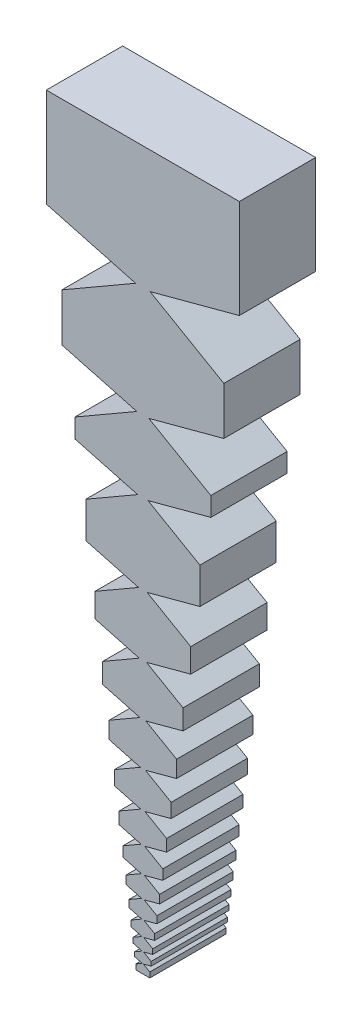
SolidWorks part; units mm, degrees
ref_plane "Front Plane" through (0, 0, 0) normal (0, 0, 1) x (1, 0, 0)
ref_plane "Top Plane" through (0, 0, 0) normal (0, 1, 0) x (1, 0, 0)
ref_plane "Right Plane" through (0, 0, 0) normal (1, 0, 0) x (0, 0, -1)
sketch "spiral_flat" plane through (0, 0, 0) normal (0, 0, 1) x (1, 0, 0)
  line L0 (0, 93.979) -> (0, 0) construction
  line L1 (0.9137, 0) -> (-0.9137, 0) construction
  line L2 (1.0887, 1.1616) -> (-1.0887, 1.1616) construction
  line L3 (1.2971, 2.5456) -> (-1.2971, 2.5456) construction
  line L4 (1.5454, 4.1945) -> (-1.5454, 4.1945) construction
  line L5 (1.8413, 6.1592) -> (-1.8413, 6.1592) construction
  line L6 (2.1938, 8.4999) -> (-2.1938, 8.4999) construction
  line L7 (2.6138, 11.2888) -> (-2.6138, 11.2888) construction
  line L8 (3.1142, 14.6116) -> (-3.1142, 14.6116) construction
  line L9 (3.7103, 18.5706) -> (-3.7103, 18.5706) construction
  line L10 (4.4207, 23.2874) -> (-4.4207, 23.2874) construction
  line L11 (5.267, 28.9073) -> (-5.267, 28.9073) construction
  line L12 (6.2753, 35.6031) -> (-6.2753, 35.6031) construction
  line L13 (7.4767, 43.5808) -> (-7.4767, 43.5808) construction
  line L14 (8.9081, 54.0582) -> (-8.9081, 54.0582) construction
  line L15 (10.6135, 63.438) -> (-10.6135, 63.438) construction
  line L16 (12.6455, 77.9031) -> (-12.6455, 77.9031) construction
  line L17 (15.0664, 93.979) -> (-15.0664, 93.979) construction
  line L18 (0, -0.6888) -> (0, 94.3287) construction
  line L19 (-0.9137, 0) -> (-15.0664, 93.979) construction
  line L20 (-12.6455, 77.9031) -> (-12.6455, 93.979) construction
  line L21 (-10.6135, 63.438) -> (-10.6135, 77.9031) construction
  line L22 (-8.9081, 54.0582) -> (-8.9081, 63.438) construction
  line L23 (-7.4767, 43.5808) -> (-7.4767, 54.0582) construction
  line L24 (-6.2753, 35.6031) -> (-6.2753, 43.5808) construction
  line L25 (-5.267, 28.9073) -> (-5.267, 35.6031) construction
  line L26 (-4.4207, 23.2874) -> (-4.4207, 28.9073) construction
  line L27 (-3.7103, 18.5706) -> (-3.7103, 23.2874) construction
  line L28 (-3.1142, 14.6116) -> (-3.1142, 18.5706) construction
  line L29 (-2.6138, 11.2888) -> (-2.6138, 14.6116) construction
  line L30 (-2.1938, 8.4999) -> (-2.1938, 11.2888) construction
  line L31 (-1.8413, 6.1592) -> (-1.8413, 8.4999) construction
  line L32 (-1.5454, 4.1945) -> (-1.5454, 6.1592) construction
  line L33 (-1.2971, 2.5456) -> (-1.2971, 4.1945) construction
  line L34 (-1.0887, 1.1616) -> (-1.0887, 2.5456) construction
  line L35 (-0.9137, 0) -> (-0.9137, 1.1616) construction
  line L36 (0.9137, 0) -> (0.9137, 1.1616) construction
  line L37 (1.0887, 1.1616) -> (1.0887, 2.5456) construction
  line L38 (1.2971, 2.5456) -> (1.2971, 4.1945) construction
  line L39 (1.5454, 4.1945) -> (1.5454, 6.1592) construction
  line L40 (1.8413, 6.1592) -> (1.8413, 8.4999) construction
  line L41 (2.1938, 8.4999) -> (2.1938, 11.2888) construction
  line L42 (2.6138, 11.2888) -> (2.6138, 14.6116) construction
  line L43 (3.1142, 14.6116) -> (3.1142, 18.5706) construction
  line L44 (3.7103, 18.5706) -> (3.7103, 23.2874) construction
  line L45 (4.4207, 23.2874) -> (4.4207, 28.9073) construction
  line L46 (5.267, 28.9073) -> (5.267, 35.6031) construction
  line L47 (6.2753, 35.6031) -> (6.2753, 43.5808) construction
  line L48 (7.4767, 43.5808) -> (7.4767, 54.0582) construction
  line L49 (8.9081, 54.0582) -> (8.9081, 63.438) construction
  line L50 (10.6135, 63.438) -> (10.6135, 77.9031) construction
  line L51 (12.6455, 77.9031) -> (12.6455, 93.979) construction
  line L52 (0.9137, 0) -> (15.0664, 93.979) construction
  line L53 (-0.0685, 0) -> (-1.13, 93.979) construction
  line L54 (0.0685, 0) -> (1.13, 93.979) construction
  line L55 (-0.9484, 77.9031) -> (-12.6455, 81.0374) construction
  line L56 (-0.9484, 77.9031) -> (-10.6135, 72.323) construction
  line L57 (-0.785, 63.438) -> (-10.6135, 66.0715) construction
  line L58 (-0.785, 63.438) -> (-8.9081, 58.7481) construction
  line L59 (-0.6791, 54.0582) -> (-8.9081, 56.2632) construction
  line L60 (-0.6791, 54.0582) -> (-7.4767, 50.1336) construction
  line L61 (-0.5608, 43.5808) -> (-7.4767, 45.4339) construction
  line L62 (-0.5608, 43.5808) -> (-6.2753, 40.2815) construction
  line L63 (-0.4707, 35.6031) -> (-6.2753, 37.1585) construction
  line L64 (-0.4707, 35.6031) -> (-5.267, 32.834) construction
  line L65 (-0.395, 28.9073) -> (-5.267, 30.2128) construction
  line L66 (-0.395, 28.9073) -> (-4.4207, 26.5831) construction
  line L67 (-0.3317, 23.2874) -> (-4.4207, 24.3831) construction
  line L68 (-0.3317, 23.2874) -> (-3.7103, 21.3368) construction
  line L69 (-0.2787, 18.5706) -> (-3.7103, 19.4901) construction
  line L70 (-0.2787, 18.5706) -> (-3.1142, 16.9335) construction
  line L71 (-0.2336, 14.6116) -> (-3.1142, 15.3835) construction
  line L72 (-0.2336, 14.6116) -> (-2.6138, 13.2374) construction
  line L73 (-0.196, 11.2888) -> (-2.6138, 11.9367) construction
  line L74 (-0.196, 11.2888) -> (-2.1938, 10.1354) construction
  line L75 (-0.1648, 8.4999) -> (-2.1938, 9.0436) construction
  line L76 (-0.1648, 8.4999) -> (-1.8413, 7.532) construction
  line L77 (-0.1382, 6.1592) -> (-1.8413, 6.6155) construction
  line L78 (-0.1382, 6.1592) -> (-1.5454, 5.3468) construction
  line L79 (-0.1159, 4.1945) -> (-1.5454, 4.5776) construction
  line L80 (-0.1159, 4.1945) -> (-1.2971, 3.5126) construction
  line L81 (-0.0973, 2.5456) -> (-1.2971, 2.8671) construction
  line L82 (-0.0973, 2.5456) -> (-1.0887, 1.9733) construction
  line L83 (-0.0816, 1.1616) -> (-1.0887, 1.4314) construction
  line L84 (-0.0816, 1.1616) -> (-0.9137, 0.6812) construction
  line L85 (0.0816, 1.1616) -> (0.9137, 0.6812) construction
  line L86 (0.0816, 1.1616) -> (1.0887, 1.4314) construction
  line L87 (0.0973, 2.5456) -> (1.0887, 1.9733) construction
  line L88 (0.0973, 2.5456) -> (1.2971, 2.8671) construction
  line L89 (0.1159, 4.1945) -> (1.2971, 3.5126) construction
  line L90 (0.1159, 4.1945) -> (1.5454, 4.5776) construction
  line L91 (0.1382, 6.1592) -> (1.5454, 5.3468) construction
  line L92 (0.1382, 6.1592) -> (1.8413, 6.6155) construction
  line L93 (0.1648, 8.4999) -> (1.8413, 7.532) construction
  line L94 (0.1648, 8.4999) -> (2.1938, 9.0436) construction
  line L95 (0.196, 11.2888) -> (2.1938, 10.1354) construction
  line L96 (0.196, 11.2888) -> (2.6138, 11.9367) construction
  line L97 (0.2336, 14.6116) -> (2.6138, 13.2374) construction
  line L98 (0.2336, 14.6116) -> (3.1142, 15.3835) construction
  line L99 (0.2787, 18.5706) -> (3.1142, 16.9335) construction
  line L100 (0.2787, 18.5706) -> (3.7103, 19.4901) construction
  line L101 (0.3317, 23.2874) -> (3.7103, 21.3368) construction
  line L102 (0.3317, 23.2874) -> (4.4207, 24.3831) construction
  line L103 (0.395, 28.9073) -> (4.4207, 26.5831) construction
  line L104 (0.395, 28.9073) -> (5.267, 30.2128) construction
  line L105 (0.4707, 35.6031) -> (5.267, 32.834) construction
  line L106 (0.4707, 35.6031) -> (6.2753, 37.1585) construction
  line L107 (0.5608, 43.5808) -> (6.2753, 40.2815) construction
  line L108 (0.5608, 43.5808) -> (7.4767, 45.4339) construction
  line L109 (0.6791, 54.0582) -> (7.4767, 50.1336) construction
  line L110 (0.6791, 54.0582) -> (8.9081, 56.2632) construction
  line L111 (0.785, 63.438) -> (8.9081, 58.7481) construction
  line L112 (0.785, 63.438) -> (10.6135, 66.0715) construction
  line L113 (0.9484, 77.9031) -> (10.6135, 72.323) construction
  line L114 (0.9484, 77.9031) -> (12.6455, 81.0374) construction
  line L115 (-12.6455, 93.979) -> (12.6455, 93.979)
  line L116 (12.6455, 93.979) -> (12.6455, 81.0374)
  line L117 (12.6455, 81.0374) -> (0.9484, 77.9031)
  line L118 (0.9484, 77.9031) -> (10.6135, 72.323)
  line L119 (10.6135, 72.323) -> (10.6135, 66.0715)
  line L120 (10.6135, 66.0715) -> (0.785, 63.438)
  line L121 (0.785, 63.438) -> (8.9081, 58.7481)
  line L122 (8.9081, 58.7481) -> (8.9081, 56.2632)
  line L123 (8.9081, 56.2632) -> (0.6791, 54.0582)
  line L124 (0.6791, 54.0582) -> (7.4767, 50.1336)
  line L125 (7.4767, 50.1336) -> (7.4767, 45.4339)
  line L126 (7.4767, 45.4339) -> (0.5608, 43.5808)
  line L127 (0.5608, 43.5808) -> (6.2753, 40.2815)
  line L128 (6.2753, 40.2815) -> (6.2753, 37.1585)
  line L129 (6.2753, 37.1585) -> (0.4707, 35.6031)
  line L130 (0.4707, 35.6031) -> (5.267, 32.834)
  line L131 (5.267, 32.834) -> (5.267, 30.2128)
  line L132 (5.267, 30.2128) -> (0.395, 28.9073)
  line L133 (0.395, 28.9073) -> (4.4207, 26.5831)
  line L134 (4.4207, 26.5831) -> (4.4207, 24.3831)
  line L135 (4.4207, 24.3831) -> (0.3317, 23.2874)
  line L136 (0.3317, 23.2874) -> (3.7103, 21.3368)
  line L137 (3.7103, 21.3368) -> (3.7103, 19.4901)
  line L138 (3.7103, 19.4901) -> (0.2787, 18.5706)
  line L139 (0.2787, 18.5706) -> (3.1142, 16.9335)
  line L140 (3.1142, 16.9335) -> (3.1142, 15.3835)
  line L141 (3.1142, 15.3835) -> (0.2336, 14.6116)
  line L142 (0.2336, 14.6116) -> (2.6138, 13.2374)
  line L143 (2.6138, 13.2374) -> (2.6138, 11.9367)
  line L144 (2.6138, 11.9367) -> (0.196, 11.2888)
  line L145 (0.196, 11.2888) -> (2.1938, 10.1354)
  line L146 (2.1938, 10.1354) -> (2.1938, 9.0436)
  line L147 (2.1938, 9.0436) -> (0.1648, 8.4999)
  line L148 (0.1648, 8.4999) -> (1.8413, 7.532)
  line L149 (1.8413, 7.532) -> (1.8413, 6.6155)
  line L150 (1.8413, 6.6155) -> (0.1382, 6.1592)
  line L151 (0.1382, 6.1592) -> (1.5454, 5.3468)
  line L152 (1.5454, 5.3468) -> (1.5454, 4.5776)
  line L153 (1.5454, 4.5776) -> (0.1159, 4.1945)
  line L154 (0.1159, 4.1945) -> (1.2971, 3.5126)
  line L155 (1.2971, 3.5126) -> (1.2971, 2.8671)
  line L156 (1.2971, 2.8671) -> (0.0973, 2.5456)
  line L157 (0.0973, 2.5456) -> (1.0887, 1.9733)
  line L158 (1.0887, 1.9733) -> (1.0887, 1.4314)
  line L159 (1.0887, 1.4314) -> (0.0816, 1.1616)
  line L160 (0.0816, 1.1616) -> (0.9137, 0.6812)
  line L161 (0.9137, 0.6812) -> (0.9137, 0)
  line L162 (0.9137, 0) -> (-0.9137, 0)
  line L163 (-0.9137, 0.6812) -> (-0.9137, 0)
  line L164 (-0.0816, 1.1616) -> (-0.9137, 0.6812)
  line L165 (-1.0887, 1.4314) -> (-0.0816, 1.1616)
  line L166 (-1.0887, 1.9733) -> (-1.0887, 1.4314)
  line L167 (-0.0973, 2.5456) -> (-1.0887, 1.9733)
  line L168 (-1.2971, 2.8671) -> (-0.0973, 2.5456)
  line L169 (-1.2971, 3.5126) -> (-1.2971, 2.8671)
  line L170 (-0.1159, 4.1945) -> (-1.2971, 3.5126)
  line L171 (-1.5454, 4.5776) -> (-0.1159, 4.1945)
  line L172 (-1.5454, 5.3468) -> (-1.5454, 4.5776)
  line L173 (-0.1382, 6.1592) -> (-1.5454, 5.3468)
  line L174 (-1.8413, 6.6155) -> (-0.1382, 6.1592)
  line L175 (-1.8413, 7.532) -> (-1.8413, 6.6155)
  line L176 (-0.1648, 8.4999) -> (-1.8413, 7.532)
  line L177 (-2.1938, 9.0436) -> (-0.1648, 8.4999)
  line L178 (-2.1938, 10.1354) -> (-2.1938, 9.0436)
  line L179 (-0.196, 11.2888) -> (-2.1938, 10.1354)
  line L180 (-2.6138, 11.9367) -> (-0.196, 11.2888)
  line L181 (-0.2336, 14.6116) -> (-2.6138, 13.2374)
  line L182 (-3.1142, 15.3835) -> (-0.2336, 14.6116)
  line L183 (-3.1142, 16.9335) -> (-3.1142, 15.3835)
  line L184 (-0.2787, 18.5706) -> (-3.1142, 16.9335)
  line L185 (-3.7103, 19.4901) -> (-0.2787, 18.5706)
  line L186 (-3.7103, 21.3368) -> (-3.7103, 19.4901)
  line L187 (-0.3317, 23.2874) -> (-3.7103, 21.3368)
  line L188 (-4.4207, 24.3831) -> (-0.3317, 23.2874)
  line L189 (-0.395, 28.9073) -> (-4.4207, 26.5831)
  line L190 (-5.267, 30.2128) -> (-0.395, 28.9073)
  line L191 (-5.267, 32.834) -> (-5.267, 30.2128)
  line L192 (-0.4707, 35.6031) -> (-5.267, 32.834)
  line L193 (-6.2753, 37.1585) -> (-0.4707, 35.6031)
  line L194 (-6.2753, 40.2815) -> (-6.2753, 37.1585)
  line L195 (-0.5608, 43.5808) -> (-6.2753, 40.2815)
  line L196 (-7.4767, 45.4339) -> (-0.5608, 43.5808)
  line L197 (-7.4767, 50.1336) -> (-7.4767, 45.4339)
  line L198 (-0.6791, 54.0582) -> (-7.4767, 50.1336)
  line L199 (-8.9081, 56.2632) -> (-0.6791, 54.0582)
  line L200 (-8.9081, 58.7481) -> (-8.9081, 56.2632)
  line L201 (-0.785, 63.438) -> (-8.9081, 58.7481)
  line L202 (-10.6135, 66.0715) -> (-0.785, 63.438)
  line L203 (-10.6135, 72.323) -> (-10.6135, 66.0715)
  line L204 (-0.9484, 77.9031) -> (-10.6135, 72.323)
  line L205 (-12.6455, 81.0374) -> (-0.9484, 77.9031)
  line L206 (-12.6455, 93.979) -> (-12.6455, 81.0374)
  line L207 (-4.4207, 26.5831) -> (-4.4207, 24.3831)
  line L208 (-2.6138, 13.2374) -> (-2.6138, 11.9367)
  spline S0 degree 3 poles (0, 0) (0, 0.3872) (0, 1.2357) (0, 2.6339) (0, 4.2998) (0, 6.2846) (0, 8.6493) (0, 11.4668) (0, 14.8237) (0, 18.8232) (0, 23.5884) (0, 29.266) (0, 36.0304) (0, 44.4141) (0, 53.6923) (0, 65.1331) (0, 78.44) (0, 88.6204) (0, 93.979) knots 0 0 0 0 0.01236 0.027087 0.044633 0.065538 0.090445 0.120121 0.155478 0.197604 0.247794 0.307594 0.378841 0.463729 0.575216 0.675023 0.828942 1 1 1 1
  point P54 (0, 1.1616)
  point P55 (0, 2.5456)
  point P56 (0, 4.1945)
  point P57 (0, 6.1592)
  point P58 (0, 8.4999)
  point P59 (0, 11.2888)
  point P60 (0, 14.6116)
  point P61 (0, 18.5706)
  point P62 (0, 23.2874)
  point P63 (0, 28.9073)
  point P64 (0, 35.6031)
  point P65 (0, 43.5808)
  point P66 (0, 54.0582)
  point P67 (0, 63.438)
  point P68 (0, 77.9031)
  point P101 (-1.13, 93.979)
  point P102 (-0.0685, 0)
  point P103 (0.0685, 0)
  point P104 (1.13, 93.979)
  point P109 (-0.9484, 77.9031)
  point P110 (-0.785, 63.438)
  point P111 (-0.6791, 54.0582)
  point P112 (-0.5608, 43.5808)
  point P113 (-0.4707, 35.6031)
  point P114 (-0.395, 28.9073)
  point P115 (-0.3317, 23.2874)
  point P116 (-0.2787, 18.5706)
  point P117 (-0.2336, 14.6116)
  point P118 (-0.196, 11.2888)
  point P119 (-0.1648, 8.4999)
  point P120 (-0.1382, 6.1592)
  point P121 (-0.1159, 4.1945)
  point P122 (-0.0973, 2.5456)
  point P123 (-0.0816, 1.1616)
  point P124 (0.9484, 77.9031)
  point P125 (0.785, 63.438)
  point P126 (0.6791, 54.0582)
  point P127 (0.5608, 43.5808)
  point P128 (0.4707, 35.6031)
  point P129 (0.395, 28.9073)
  point P130 (0.3317, 23.2874)
  point P131 (0.2787, 18.5706)
  point P132 (0.2336, 14.6116)
  point P133 (0.196, 11.2888)
  point P134 (0.1648, 8.4999)
  point P135 (0.1382, 6.1592)
  point P136 (0.1159, 4.1945)
  point P137 (0.0973, 2.5456)
  point P138 (0.0816, 1.1616)
  dimension "D1" = 1.8275
  dimension "D2" = 2.1773
  dimension "D3" = 2.5942
  dimension "D4" = 3.0908
  dimension "D5" = 3.6825
  dimension "D6" = 4.3875
  dimension "D7" = 5.2275
  dimension "D8" = 6.2283
  dimension "D9" = 7.4207
  dimension "D10" = 8.8414
  dimension "D11" = 10.534
  dimension "D12" = 12.5507
  dimension "D13" = 14.9535
  dimension "D14" = 17.8162
  dimension "D15" = 21.2271
  dimension "D16" = 25.2909
  dimension "D17" = 30.1328
  dimension "D18" = 0.1371
  dimension "D19" = 2.26
  dimension "D20" = 15
  dimension "D21" = 30
  dimension "D22" = 15
  dimension "D23" = 30
  dimension "D24" = 15
  dimension "D25" = 30
  dimension "D26" = 15
  dimension "D27" = 30
  dimension "D28" = 15
  dimension "D29" = 30
  dimension "D30" = 15
  dimension "D31" = 30
  dimension "D32" = 15
  dimension "D33" = 30
  dimension "D34" = 15
  dimension "D35" = 30
  dimension "D36" = 15
  dimension "D37" = 30
  dimension "D38" = 15
  dimension "D39" = 30
  dimension "D40" = 15
  dimension "D41" = 30
  dimension "D42" = 15
  dimension "D43" = 30
  dimension "D44" = 15
  dimension "D45" = 30
  dimension "D46" = 15
  dimension "D47" = 30
  dimension "D48" = 15
  dimension "D49" = 30
extrude "Boss-Extrude1" add sketch "spiral_flat" along normal blind 10 contours L162 S0 L115 L206 L205 L204 L203 L202 L201 L200 L199 L198 L197 L196 L195 L194 L193 L192 L191 L190 L189 L207 L188 L187 L186 L185 L184 L183 L182 L181 L208 L180 L179 L178 L177 L176 L175 L174 L173 L172 L171 L170 L169 L168 L167 L166 L165 L164 L163 | S0 L162 L161 L160 L159 L158 L157 L156 L155 L154 L153 L152 L151 L150 L149 L148 L147 L146 L145 L144 L143 L142 L141 L140 L139 L138 L137 L136 L135 L134 L133 L132 L131 L130 L129 L128 L127 L126 L125 L124 L123 L122 L121 L120 L119 L118 L117 L116 L115
sketch "Sketch24" plane through (0, 0, 0) normal (0, -1, 0) x (1, 0, 0)
  line L0 (0, 10) -> (0, 0) construction
  line L1 (0.9137, 10) -> (-0.9137, 10) construction
  line L2 (-0.9137, 5) -> (0.9137, 5) construction
  line L3 (-0.9137, 10) -> (-0.9137, 0) construction
  line L4 (0.9137, 10) -> (0.9137, 0) construction
  line L5 (0, 6) -> (0.9137, 6) construction
  line L6 (0, 6) -> (0.9137, 5.7552) construction
  line L7 (0, 6) -> (-0.9137, 5.7552) construction
  line L8 (0, 4) -> (-0.9137, 4.2448) construction
  line L9 (0, 4) -> (0.9137, 4.2448) construction
  line L10 (0, 6) -> (0.9137, 5.7552)
  line L11 (0.9137, 5.7552) -> (0.9137, 4.2448)
  line L12 (0.9137, 4.2448) -> (0, 4)
  line L13 (0, 4) -> (-0.9137, 4.2448)
  line L14 (-0.9137, 4.2448) -> (-0.9137, 5.7552)
  line L15 (-0.9137, 5.7552) -> (0, 6)
  point P11 (0, 6)
  point P12 (0, 4)
  dimension "D1" = 2
  dimension "D2" = 15
sketch "Sketch25" plane through (0, 93.979, 0) normal (0, 1, 0) x (1, 0, 0)
  line L0 (0, 0) -> (0, -10) construction
  line L1 (-12.6455, -5) -> (12.6455, -5) construction
  line L2 (-12.6455, -10) -> (-12.6455, 0) construction
  line L3 (12.6455, -10) -> (12.6455, 0) construction
  line L4 (0, 0) -> (-12.6455, -2.2297) construction
  line L5 (0, 0) -> (12.6455, -2.2297) construction
  line L6 (-12.6455, 0) -> (12.6455, 0) construction
  line L7 (0, -10) -> (12.6455, -7.7703) construction
  line L8 (0, -10) -> (-12.6455, -7.7703) construction
  line L9 (0, 0) -> (-12.6455, -2.2297)
  line L10 (-12.6455, -2.2297) -> (-12.6455, -7.7703)
  line L11 (-12.6455, -7.7703) -> (0, -10)
  line L12 (0, -10) -> (12.6455, -7.7703)
  line L13 (12.6455, -7.7703) -> (12.6455, -2.2297)
  line L14 (12.6455, -2.2297) -> (0, 0)
  point P16 (0, -5)
  point P17 (6.3227, -5)
  point P18 (-9.4841, -5)
  point P19 (-6.3227, -5)
  point P20 (9.4841, -5)
  point P21 (11.0648, -5)
  point P22 (-11.0648, -5)
  dimension "D1" = 10
  dimension "D2" = 10
  dimension "D3" = 6.3227
  dimension "D4" = 3.1614
  dimension "D5" = 1.5807
equation "\"mm\"=0.476787"
